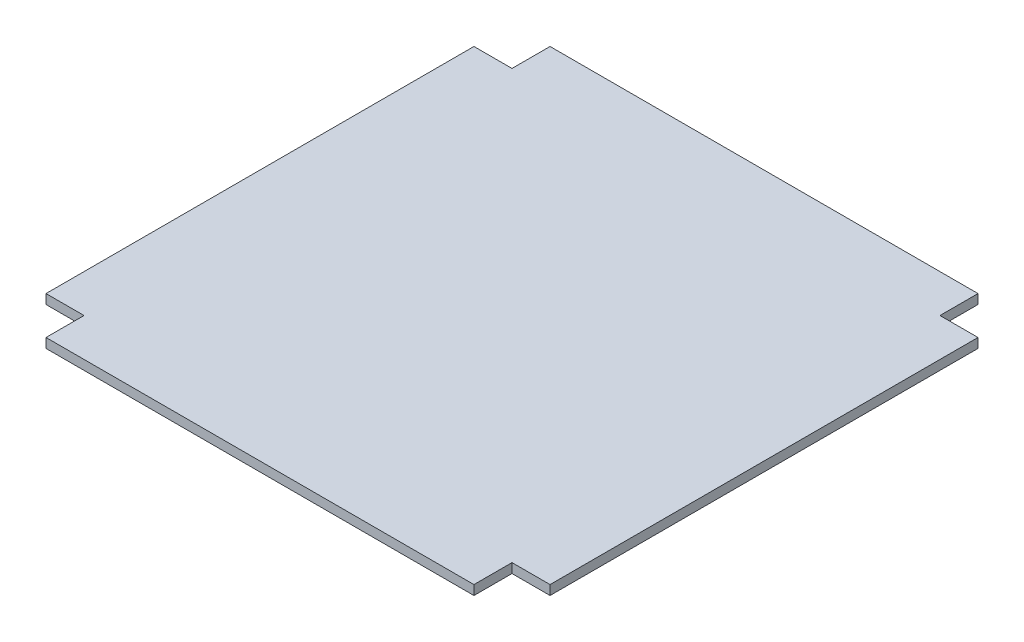
SolidWorks part; units mm, degrees
ref_plane "Front Plane" through (0, 0, 0) normal (0, 0, 1) x (1, 0, 0)
ref_plane "Top Plane" through (0, 0, 0) normal (0, 1, 0) x (1, 0, 0)
ref_plane "Right Plane" through (0, 0, 0) normal (1, 0, 0) x (0, 0, -1)
sketch "Sketch1" plane through (0, 0, 0) normal (0, 1, 0) x (1, 0, 0)
  line L1 (-265, -265) -> (265, -265)
  line L2 (-265, -265) -> (-265, 265)
  line L3 (-265, 265) -> (265, 265)
  line L4 (265, -265) -> (265, 265)
  line L5 (-265, -265) -> (265, 265) construction
  line L6 (-265, 265) -> (265, -265) construction
  point P0 (0, 0)
  dimension "D1" = 530
  dimension "D2" = 530
extrude "Boss-Extrude1" add sketch "Sketch1" along normal blind 10
sketch "Sketch2" plane through (0, 10, 0) normal (0, 1, 0) x (1, 0, 0)
  line L1 (-265, 265) -> (-225, 265)
  line L2 (-265, 265) -> (-265, 225)
  line L3 (-265, 225) -> (-225, 225)
  line L4 (-225, 265) -> (-225, 225)
  line L5 (265, 265) -> (225, 265)
  line L6 (265, 265) -> (265, 225)
  line L7 (265, 225) -> (225, 225)
  line L8 (225, 265) -> (225, 225)
  line L9 (-265, -265) -> (-225, -265)
  line L10 (-265, -265) -> (-265, -225)
  line L11 (-265, -225) -> (-225, -225)
  line L12 (-225, -265) -> (-225, -225)
  line L13 (265, -265) -> (225, -265)
  line L14 (265, -265) -> (265, -225)
  line L15 (265, -225) -> (225, -225)
  line L16 (225, -265) -> (225, -225)
  dimension "D1" = 40
  dimension "D2" = 40
  dimension "D3" = 40
  dimension "D4" = 40
  dimension "D5" = 40
  dimension "D6" = 40
  dimension "D7" = 40
  dimension "D8" = 40
extrude "Cut-Extrude1" cut sketch "Sketch2" against normal through all
